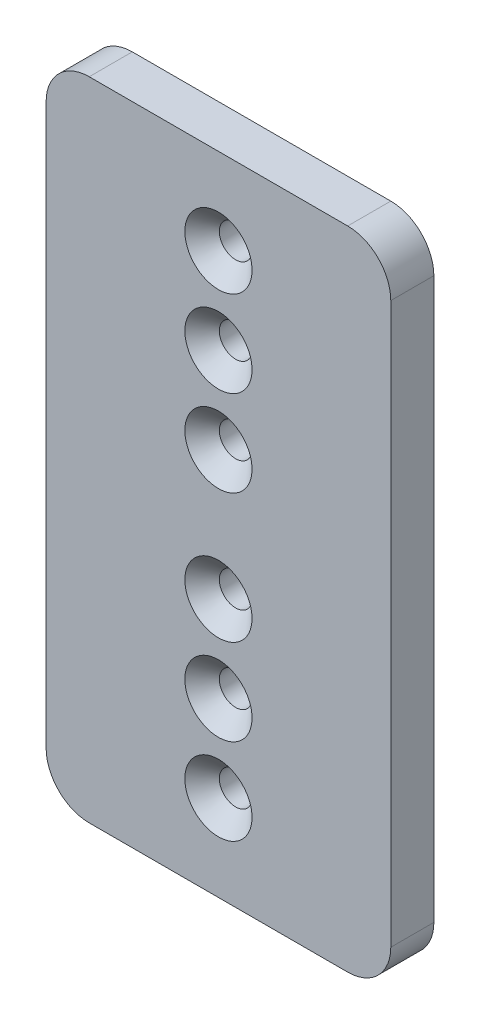
SolidWorks part; units mm, degrees
material "6061-T6 (SS)"
ref_plane "Front Plane" through (0, 0, 0) normal (0, 0, 1) x (1, 0, 0)
ref_plane "Top Plane" through (0, 0, 0) normal (0, 1, 0) x (1, 0, 0)
ref_plane "Right Plane" through (0, 0, 0) normal (1, 0, 0) x (0, 0, -1)
sketch "Sketch1" plane through (0, 0, 0) normal (0, 0, 1) x (1, 0, 0)
  line L0 (25.4, 95.25) -> (25.4, 0) construction
  line L1 (0, 0) -> (50.8, 0)
  line L2 (0, 0) -> (0, 95.25)
  line L3 (0, 95.25) -> (50.8, 95.25)
  line L4 (50.8, 0) -> (50.8, 95.25)
  circle A0 centre (25.4, 69.85) radius 2.413
  circle A1 centre (25.4, 25.4) radius 2.413
  circle A2 centre (25.4, 57.15) radius 2.413
  circle A3 centre (25.4, 12.7) radius 2.413
  circle A4 centre (25.4, 38.1) radius 2.413
  circle A5 centre (25.4, 82.55) radius 2.413
  dimension "D3" = 44.45
  dimension "D5" = 4.826
  dimension "D1" = 95.25
  dimension "D2" = 50.8
  dimension "D4" = 25.4
  dimension "D6" = 12.7
  dimension "D7" = 12.7
  dimension "D8" = 12.7
  dimension "D9" = 12.7
extrude "Boss-Extrude1" add sketch "Sketch1" along normal blind 6.35
fillet "Fillet1" radius 6.35 4 edges at (0, 0, 3.175) (50.8, 0, 3.175) (50.8, 95.25, 3.175) (0, 95.25, 3.175)
chamfer "Chamfer1" distance 2.54 angle 45 6 edges at (27.813, 25.4, 6.35) (27.813, 69.85, 6.35) (27.813, 12.7, 6.35) (27.813, 82.55, 6.35) (27.813, 57.15, 6.35) (27.813, 38.1, 6.35)
